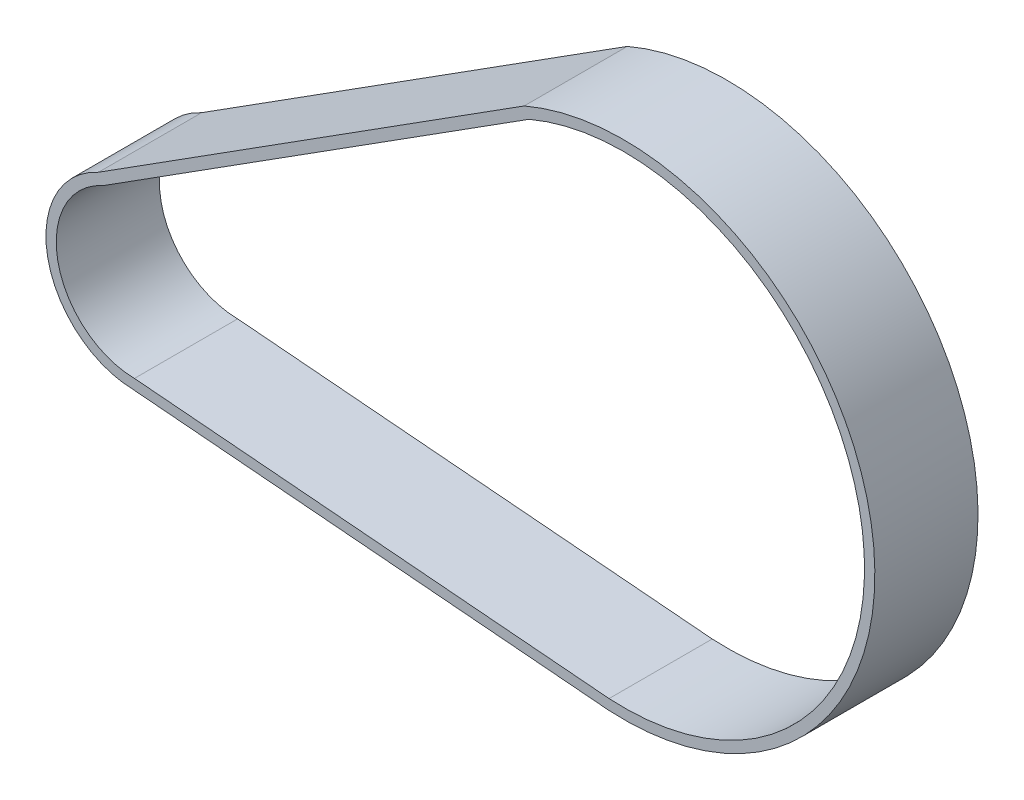
SolidWorks part; units mm, degrees
material "Rubber"
ref_plane "Front Plane" through (0, 0, 0) normal (0, 0, 1) x (1, 0, 0)
ref_plane "Top Plane" through (0, 0, 0) normal (0, 1, 0) x (1, 0, 0)
ref_plane "Right Plane" through (0, 0, 0) normal (1, 0, 0) x (0, 0, -1)
sketch "Sketch1" plane through (0, 0, 0) normal (0, 0, 1) x (1, 0, 0)
  line L0 (-4.655, 10.5158) -> (57.2304, 49.8037)
  line L5 (68.8644, -17.3068) -> (-0.1308, -11.4993)
  line L6 (-5.3673, 11.8403) -> (56.5277, 51.1343)
  line L7 (68.7555, -18.803) -> (-0.204, -12.9984)
  arc A4 (-4.655, 10.5158) -> (-0.1308, -11.4993) centre (0, 0) ccw
  arc A5 (68.8644, -17.3068) -> (57.2304, 49.8037) centre (71.0038, 17.6277) ccw
  arc A6 (68.7555, -18.803) -> (56.5277, 51.1343) centre (71.0038, 17.6277) ccw
  arc A7 (-5.3673, 11.8403) -> (-0.204, -12.9984) centre (0, 0) ccw
  point P6 (68.7555, -17.3068)
  dimension "D1" = 300
  dimension "D2" = 35
  dimension "D3" = 11.5
  dimension "D4" = 1.5
extrude "Boss-Extrude1" add sketch "Sketch1" along normal blind 15
